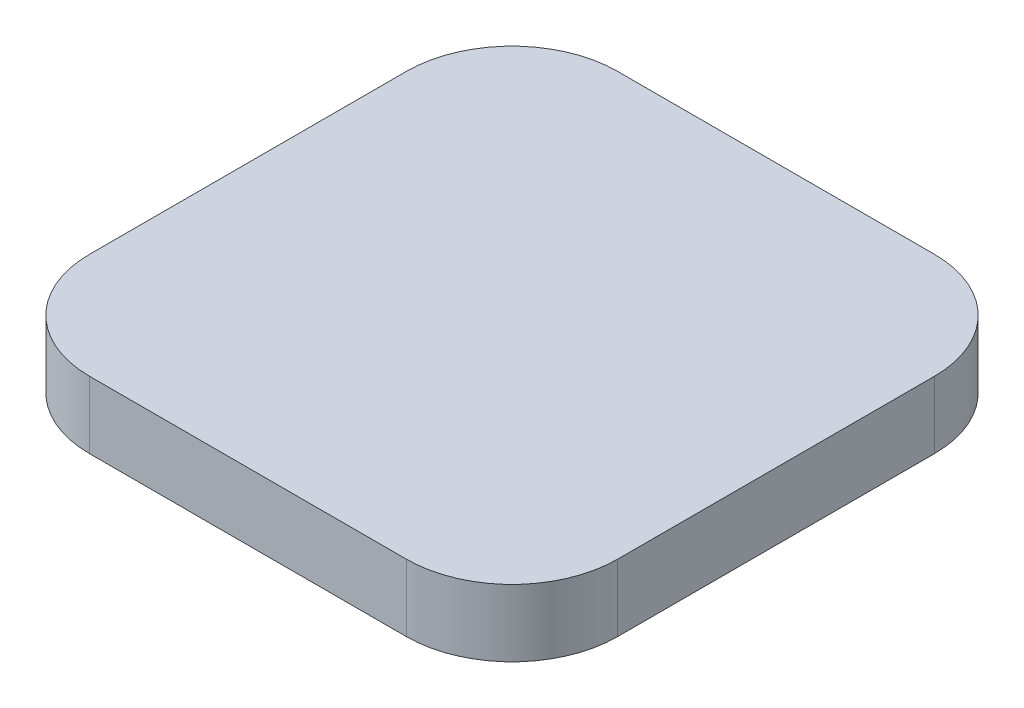
SolidWorks part; units mm, degrees
material "Glass"
ref_plane "Front Plane" through (0, 0, 0) normal (0, 0, 1) x (1, 0, 0)
ref_plane "Top Plane" through (0, 0, 0) normal (0, 1, 0) x (1, 0, 0)
ref_plane "Right Plane" through (0, 0, 0) normal (1, 0, 0) x (0, 0, -1)
sketch "Sketch1" plane through (0, 0, 0) normal (0, 1, 0) x (1, 0, 0)
  line L1 (0, 0) -> (25, 0)
  line L2 (0, 0) -> (0, -25)
  line L3 (0, -25) -> (25, -25)
  line L4 (25, 0) -> (25, -25)
  dimension "D1" = 25
  dimension "D2" = 25
extrude "Boss-Extrude1" add sketch "Sketch1" along normal blind 3.175
fillet "Fillet1" radius 5 4 edges at (0, 1.5875, 0) (0, 1.5875, 25) (25, 1.5875, 0) (25, 1.5875, 25)
